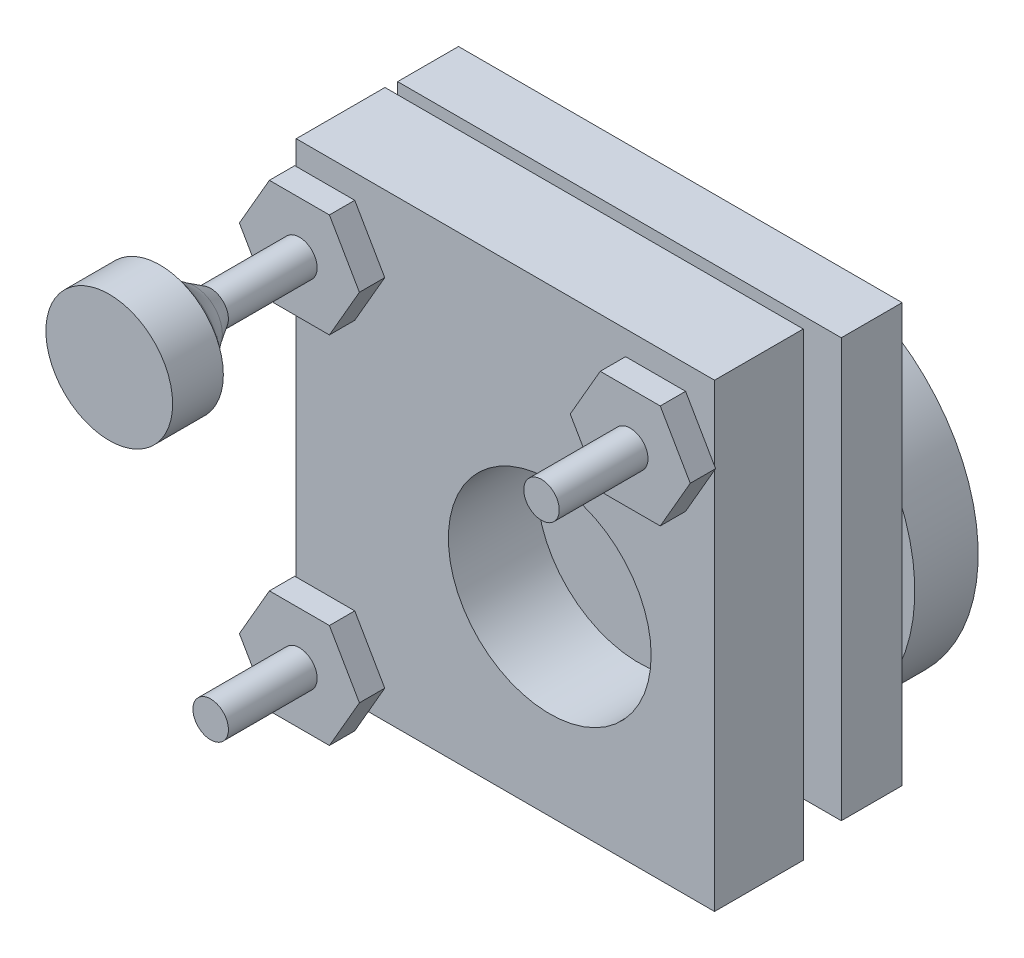
SolidWorks part; units mm, degrees
ref_plane "Alzado" through (0, 0, 0) normal (0, 0, 1) x (1, 0, 0)
ref_plane "Planta" through (0, 0, 0) normal (0, 1, 0) x (1, 0, 0)
ref_plane "Vista lateral" through (0, 0, 0) normal (1, 0, 0) x (0, 0, -1)
sketch "Croquis1" plane through (0, 0, 0) normal (0, 1, 0) x (1, 0, 0)
  line L1 (-16.5, -3.5) -> (16.5, -3.5)
  line L2 (-16.5, -3.5) -> (-16.5, 3.5)
  line L3 (-16.5, 3.5) -> (16.5, 3.5)
  line L4 (16.5, -3.5) -> (16.5, 3.5)
  line L5 (-16.5, -3.5) -> (16.5, 3.5) construction
  line L6 (-16.5, 3.5) -> (16.5, -3.5) construction
  point P0 (0, 0)
  dimension "D1" = 7
  dimension "D2" = 33
extrude "Saliente-Extruir1" add sketch "Croquis1" along normal blind 36.3
sketch "Croquis2" plane through (0, 0, 0) normal (0, -1, 0) x (1, 0, 0)
  line L0 (16.5, 3.5) -> (16.5, -3.5) construction
  line L2 (-6.8, 0) -> (0, 0) construction
  circle A0 centre (-6.8, 0) radius 1.5
  circle A1 centre (9.3, 0) radius 1.5
  dimension "D1" = 3
  dimension "D3" = 16.1
  dimension "D2" = 7.2
extrude "Cortar-Extruir1" cut sketch "Croquis2" against normal blind 5
sketch "Croquis3" plane through (0, 0, 3.5) normal (0, 0, 1) x (1, 0, 0)
  line L0 (16.5, 36.3) -> (16.5, 0) construction
  line L1 (-16.5, 0) -> (16.5, 0) construction
  circle A0 centre (3.5, 15) radius 8
  dimension "D1" = 16
  dimension "D2" = 13
  dimension "D3" = 15
extrude "Cortar-Extruir2" cut sketch "Croquis3" against normal through all
sketch "Croquis4" plane through (0, 0, 3.5) normal (0, 0, 1) x (1, 0, 0)
  line L0 (-16.5, 36.3) -> (16.5, 36.3) construction
  line L1 (-16.5, 36.3) -> (-16.5, 0) construction
  line L2 (16.5, 36.3) -> (16.5, 0) construction
  line L3 (-16.5, 0) -> (16.5, 0) construction
  circle A0 centre (-13.05, 31.5) radius 2.4
  circle A1 centre (13.05, 31.5) radius 2.4
  circle A2 centre (-13.05, 3.45) radius 2.4
  dimension "D1" = 4.8
  dimension "D2" = 4.8
  dimension "D3" = 3.45
  dimension "D4" = 3.45
  dimension "D5" = 3.45
extrude "Saliente-Extruir2" add sketch "Croquis4" along normal blind 1.2
sketch "Croquis5" plane through (0, 0, 4.7) normal (0, 0, 1) x (1, 0, 0)
  line L1 (-17.7843, 31.5) -> (-15.4171, 27.4)
  line L2 (-15.4171, 27.4) -> (-10.6829, 27.4)
  line L3 (-10.6829, 27.4) -> (-8.3157, 31.5)
  line L4 (-8.3157, 31.5) -> (-10.6829, 35.6)
  line L5 (-10.6829, 35.6) -> (-15.4171, 35.6)
  line L6 (-15.4171, 35.6) -> (-17.7843, 31.5)
  line L7 (17.7843, 31.5) -> (15.4171, 35.6)
  line L8 (15.4171, 35.6) -> (10.6829, 35.6)
  line L9 (10.6829, 35.6) -> (8.3157, 31.5)
  line L10 (8.3157, 31.5) -> (10.6829, 27.4)
  line L11 (10.6829, 27.4) -> (15.4171, 27.4)
  line L12 (15.4171, 27.4) -> (17.7843, 31.5)
  line L13 (-8.3157, 3.45) -> (-10.6829, 7.55)
  line L14 (-10.6829, 7.55) -> (-15.4171, 7.55)
  line L15 (-15.4171, 7.55) -> (-17.7843, 3.45)
  line L16 (-17.7843, 3.45) -> (-15.4171, -0.65)
  line L17 (-15.4171, -0.65) -> (-10.6829, -0.65)
  line L18 (-10.6829, -0.65) -> (-8.3157, 3.45)
  circle A0 centre (-13.05, 31.5) radius 4.1 construction
  circle A1 centre (13.05, 31.5) radius 4.1 construction
  circle A2 centre (-13.05, 3.45) radius 4.1 construction
  dimension "D1" = 8.2
extrude "Saliente-Extruir3" add sketch "Croquis5" along normal blind 2
sketch "Croquis6" plane through (0, 0, 6.7) normal (0, 0, 1) x (1, 0, 0)
  line L0 (-15.4171, 35.6) -> (-10.6829, 27.4) construction
  line L1 (10.6829, 35.6) -> (15.4171, 27.4) construction
  line L3 (-15.4171, 7.55) -> (-10.6829, -0.65) construction
  circle A0 centre (-13.05, 31.5) radius 1.4
  circle A1 centre (13.05, 31.5) radius 1.4
  circle A2 centre (-13.05, 3.45) radius 1.4
  dimension "D1" = 2.8
extrude "Saliente-Extruir4" add sketch "Croquis6" along normal blind 7
sketch "Croquis7" plane through (0, 0, 6.7) normal (0, 0, 1) x (1, 0, 0)
  line L0 (-17.7843, 31.5) -> (-8.3157, 31.5)
ref_plane "Plano1" through (0, 31.5, 0) normal (0, -1, 0) x (1, 0, 0)
sketch "Croquis8" plane through (0, 31.5, 0) normal (0, -1, 0) x (1, 0, 0)
  line L0 (-14.45, 13.7) -> (-15.2324, 14.963)
  line L1 (-16.9089, 16.8202) -> (-18.05, 17.7)
  line L2 (-18.05, 17.7) -> (-18.05, 21.7)
  line L3 (-18.05, 21.7) -> (-13.05, 21.7)
  line L4 (-13.05, 21.7) -> (-13.05, 13.7) construction
  line L5 (-11.65, 13.7) -> (-14.45, 13.7) construction
  line L6 (-14.45, 13.7) -> (-13.05, 13.7)
  line L7 (-13.05, 21.7) -> (-13.05, 13.7)
  arc A0 (-15.2324, 14.963) -> (-16.9089, 16.8202) centre (-21.1831, 11.2766) ccw
  dimension "D3" = 7
  dimension "D1" = 4
  dimension "D2" = 4
  dimension "D4" = 5
revolve "Revolución1" add sketch "Croquis8" angle 360 about L4
ref_plane "Plano2" through (0, 0, -5.5) normal (0, 0, -1) x (-1, 0, 0)
sketch "Croquis9" plane through (0, 0, -5.5) normal (0, 0, -1) x (-1, 0, 0)
  line L1 (-17.5, 35.2) -> (17.5, 35.2)
  line L2 (-17.5, 35.2) -> (-17.5, 2.2)
  line L3 (-17.5, 2.2) -> (17.5, 2.2)
  line L4 (17.5, 35.2) -> (17.5, 2.2)
  line L6 (-16.5, 36.3) -> (-16.5, 0) construction
  line L8 (-16.5, 36.3) -> (16.5, 36.3) construction
  dimension "D1" = 35
  dimension "D2" = 33
  dimension "D3" = 1
  dimension "D4" = 1.1
extrude "Saliente-Extruir5" add sketch "Croquis9" along normal blind 4.8 separate body
sketch "Croquis10" plane through (0, 0, -10.3) normal (0, 0, -1) x (-1, 0, 0)
  circle A0 centre (-3.5, 15) radius 5.8397
  circle A1 centre (-3.5, 15) radius 8 construction
  dimension "D1" = 11.6793
extrude "Saliente-Extruir6" add sketch "Croquis10" along normal blind 1
sketch "Croquis11" plane through (0, 0, -11.3) normal (0, 0, -1) x (-1, 0, 0)
  circle A0 centre (-3.5, 15) radius 14
  dimension "D1" = 28
extrude "Saliente-Extruir7" add sketch "Croquis11" along normal blind 5
sketch "Croquis12" plane through (0, 0, -16.3) normal (0, 0, -1) x (-1, 0, 0)
  circle A0 centre (-3.5, 15) radius 8
  circle A1 centre (-3.5, 15) radius 14 construction
  dimension "D1" = 16
extrude "Cortar-Extruir3" cut sketch "Croquis12" against normal blind 1
ref_point "Punto1"
ref_plane "Plano3" through (0, 15, 0) normal (0, 1, 0) x (1, 0, 0)
sketch "Croquis13" plane through (0, 15, 0) normal (0, 1, 0) x (1, 0, 0)
  line L0 (3.5, 15.3) -> (-361.8579, 380.6579)
  line L1 (3.5, 15.3) -> (154.7841, 166.5841)
  line L2 (3.5, 15.3) -> (3.5, 50.4322) construction
  dimension "D1" = 90
  dimension "D2" = 45
